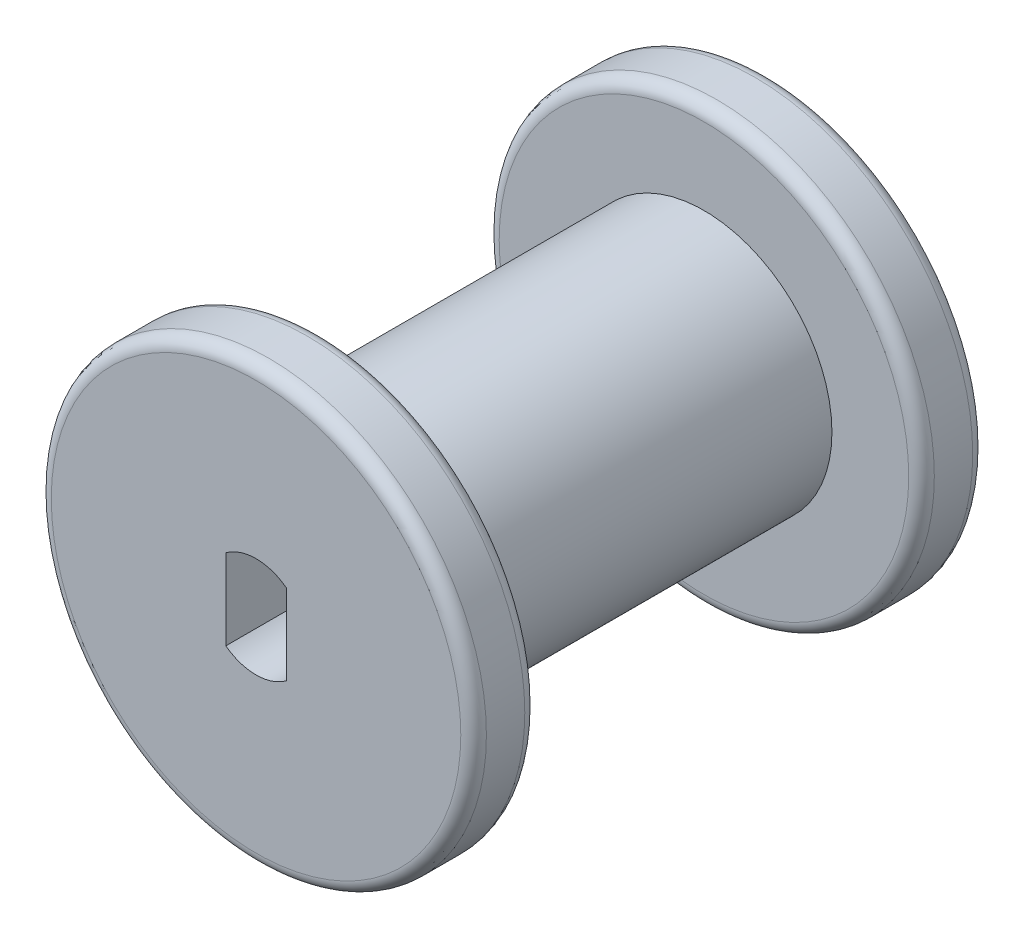
SolidWorks part; units mm, degrees
material "ABS"
ref_plane "Front Plane" through (0, 0, 0) normal (0, 0, 1) x (1, 0, 0)
ref_plane "Top Plane" through (0, 0, 0) normal (0, 1, 0) x (1, 0, 0)
ref_plane "Right Plane" through (0, 0, 0) normal (1, 0, 0) x (0, 0, -1)
sketch "Sketch1" plane through (0, 0, 0) normal (0, 0, 1) x (1, 0, 0)
  line L0 (1.5, -2) -> (1.5, 2)
  line L1 (-1.5, -2) -> (-1.5, 2)
  circle A0 centre (0, 0) radius 10.795
  arc A1 (1.5, 2) -> (-1.5, 2) centre (0, 0) ccw
  arc A2 (-1.5, -2) -> (1.5, -2) centre (0, 0) ccw
  dimension "D1" = 21.59
  dimension "D2" = 5
  dimension "D3" = 3
extrude "Boss-Extrude1" add sketch "Sketch1" along normal blind 25.4
ref_plane "Plane1" through (0, 0, 12.7) normal (0, 0, 1) x (1, 0, 0)
sketch "Sketch2" plane through (0, 0, 12.7) normal (0, 0, 1) x (1, 0, 0)
  circle A0 centre (0, 0) radius 6.35
  circle A1 centre (0, 0) radius 10.795 construction
  circle A2 centre (0, 0) radius 10.795
  dimension "D1" = 12.7
extrude "Cut-Extrude1" cut sketch "Sketch2" against normal mid plane 19.05
fillet "Fillet3" radius 0.635 4 edges at (10.795, 0, 0) (10.795, 0, 3.175) (10.795, 0, 25.4) (10.795, 0, 22.225)
